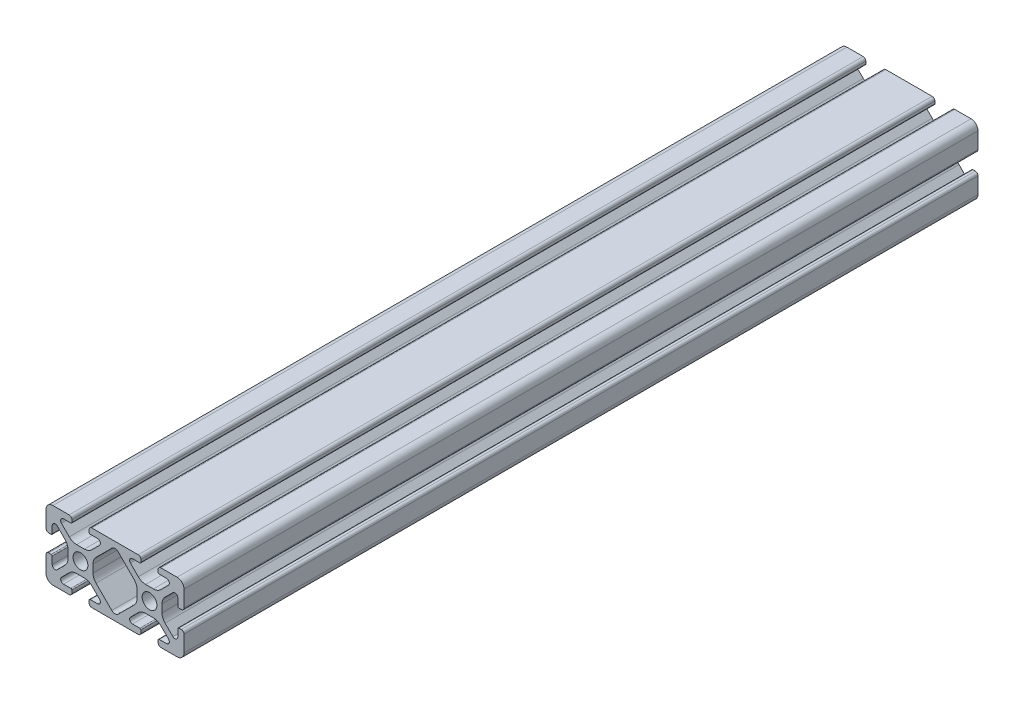
SolidWorks part; units mm, degrees
ref_plane "Front Plane" through (0, 0, 0) normal (0, 0, 1) x (1, 0, 0)
ref_plane "Top Plane" through (0, 0, 0) normal (0, 1, 0) x (1, 0, 0)
ref_plane "Right Plane" through (0, 0, 0) normal (1, 0, 0) x (0, 0, -1)
sketch "Sketch1" plane through (0, 0, 0) normal (0, 0, 1) x (1, 0, 0)
  line L2 (-19.9898, 7.9883) -> (-19.9898, 3.2893)
  line L3 (-17.9832, 9.9949) -> (-13.2842, 9.9949)
  line L4 (-12.4968, 9.2075) -> (-12.4968, 8.4963)
  line L5 (-12.8016, 8.1915) -> (-14.9098, 8.1915)
  line L6 (-15.5025, 6.7606) -> (-13.2477, 4.5058)
  line L7 (-16.7555, 5.5076) -> (-14.5007, 3.2528)
  line L8 (-18.1864, 4.9149) -> (-18.1864, 2.8067)
  line L9 (-18.4912, 2.5019) -> (-19.2024, 2.5019)
  line L11 (-11.1283, 3.6279) -> (-8.8615, 3.6279)
  line L12 (-13.6228, 1.1334) -> (-13.6228, -1.1334)
  line L13 (0, 9.9949) -> (-6.7056, 9.9949)
  line L14 (-7.493, 9.2075) -> (-7.493, 8.4963)
  line L15 (-7.1882, 8.1915) -> (-5.08, 8.1915)
  line L16 (-6.367, 1.1334) -> (-6.367, -1.1334)
  line L17 (-4.4873, 6.7606) -> (-6.7421, 4.5058)
  line L18 (-0.9396, 7.8023) -> (-5.4891, 3.2528)
  line L19 (-18.4912, -2.5019) -> (-19.2024, -2.5019)
  line L20 (-18.1864, -4.9149) -> (-18.1864, -2.8067)
  line L21 (-16.7555, -5.5076) -> (-14.5007, -3.2528)
  line L22 (-15.5025, -6.7606) -> (-13.2477, -4.5058)
  line L23 (-12.8016, -8.1915) -> (-14.9098, -8.1915)
  line L24 (-12.4968, -9.2075) -> (-12.4968, -8.4963)
  line L25 (-17.9832, -9.9949) -> (-13.2842, -9.9949)
  line L26 (-19.9898, -7.9883) -> (-19.9898, -3.2893)
  line L27 (0, -9.9949) -> (-6.7056, -9.9949)
  line L28 (-7.493, -9.2075) -> (-7.493, -8.4963)
  line L29 (-7.1882, -8.1915) -> (-5.08, -8.1915)
  line L30 (-4.4873, -6.7606) -> (-6.7421, -4.5058)
  line L31 (-0.9396, -7.8023) -> (-5.4891, -3.2528)
  line L32 (-11.1283, -3.6279) -> (-8.8615, -3.6279)
  line L34 (11.1283, -3.6279) -> (8.8615, -3.6279)
  line L35 (0.9396, -7.8023) -> (5.4891, -3.2528)
  line L36 (4.4873, -6.7606) -> (6.7421, -4.5058)
  line L37 (7.1882, -8.1915) -> (5.08, -8.1915)
  line L38 (7.493, -9.2075) -> (7.493, -8.4963)
  line L39 (0, -9.9949) -> (6.7056, -9.9949)
  line L40 (19.9898, -7.9883) -> (19.9898, -3.2893)
  line L41 (17.9832, -9.9949) -> (13.2842, -9.9949)
  line L42 (12.4968, -9.2075) -> (12.4968, -8.4963)
  line L43 (12.8016, -8.1915) -> (14.9098, -8.1915)
  line L44 (15.5025, -6.7606) -> (13.2477, -4.5058)
  line L45 (16.7555, -5.5076) -> (14.5007, -3.2528)
  line L46 (18.1864, -4.9149) -> (18.1864, -2.8067)
  line L47 (18.4912, -2.5019) -> (19.2024, -2.5019)
  line L48 (0.9396, 7.8023) -> (5.4891, 3.2528)
  line L49 (4.4873, 6.7606) -> (6.7421, 4.5058)
  line L50 (6.367, 1.1334) -> (6.367, -1.1334)
  line L51 (7.1882, 8.1915) -> (5.08, 8.1915)
  line L52 (7.493, 9.2075) -> (7.493, 8.4963)
  line L53 (0, 9.9949) -> (6.7056, 9.9949)
  line L54 (13.6228, 1.1334) -> (13.6228, -1.1334)
  line L55 (11.1283, 3.6279) -> (8.8615, 3.6279)
  line L56 (18.4912, 2.5019) -> (19.2024, 2.5019)
  line L57 (18.1864, 4.9149) -> (18.1864, 2.8067)
  line L58 (16.7555, 5.5076) -> (14.5007, 3.2528)
  line L59 (15.5025, 6.7606) -> (13.2477, 4.5058)
  line L60 (12.8016, 8.1915) -> (14.9098, 8.1915)
  line L61 (12.4968, 9.2075) -> (12.4968, 8.4963)
  line L62 (17.9832, 9.9949) -> (13.2842, 9.9949)
  line L63 (19.9898, 7.9883) -> (19.9898, 3.2893)
  circle A0 centre (-9.9949, 0) radius 2.1463
  arc A1 (-19.9898, 7.9883) -> (-17.9832, 9.9949) centre (-17.9832, 7.9883) cw
  arc A2 (-16.7555, 5.5076) -> (-18.1864, 4.9149) centre (-17.3482, 4.9149) ccw
  arc A3 (-14.9098, 8.1915) -> (-15.5025, 6.7606) centre (-14.9098, 7.3533) ccw
  arc A4 (-13.2842, 9.9949) -> (-12.4968, 9.2075) centre (-13.2842, 9.2075) cw
  arc A5 (-19.9898, 3.2893) -> (-19.2024, 2.5019) centre (-19.2024, 3.2893) ccw
  arc A6 (-18.1864, 2.8067) -> (-18.4912, 2.5019) centre (-18.4912, 2.8067) cw
  arc A7 (-12.4968, 8.4963) -> (-12.8016, 8.1915) centre (-12.8016, 8.4963) cw
  arc A8 (-11.1283, 3.6279) -> (-13.2477, 4.5058) centre (-11.1283, 6.6251) cw
  arc A9 (-13.6228, 1.1334) -> (-14.5007, 3.2528) centre (-16.62, 1.1334) ccw
  arc A10 (0.9396, 7.8023) -> (-0.9396, 7.8023) centre (0, 6.8627) ccw
  arc A11 (-0.9396, -7.8023) -> (0.9396, -7.8023) centre (0, -6.8627) ccw
  arc A12 (-6.7056, 9.9949) -> (-7.493, 9.2075) centre (-6.7056, 9.2075) ccw
  arc A13 (-7.493, 8.4963) -> (-7.1882, 8.1915) centre (-7.1882, 8.4963) ccw
  arc A14 (-8.8615, 3.6279) -> (-6.7421, 4.5058) centre (-8.8615, 6.6251) ccw
  arc A15 (-6.367, 1.1334) -> (-5.4891, 3.2528) centre (-3.3698, 1.1334) cw
  arc A16 (-5.08, 8.1915) -> (-4.4873, 6.7606) centre (-5.08, 7.3533) cw
  arc A17 (-13.6228, -1.1334) -> (-14.5007, -3.2528) centre (-16.62, -1.1334) cw
  arc A18 (-11.1283, -3.6279) -> (-13.2477, -4.5058) centre (-11.1283, -6.6251) ccw
  arc A19 (-12.4968, -8.4963) -> (-12.8016, -8.1915) centre (-12.8016, -8.4963) ccw
  arc A20 (-18.1864, -2.8067) -> (-18.4912, -2.5019) centre (-18.4912, -2.8067) ccw
  arc A21 (-19.9898, -3.2893) -> (-19.2024, -2.5019) centre (-19.2024, -3.2893) cw
  arc A22 (-13.2842, -9.9949) -> (-12.4968, -9.2075) centre (-13.2842, -9.2075) ccw
  arc A23 (-14.9098, -8.1915) -> (-15.5025, -6.7606) centre (-14.9098, -7.3533) cw
  arc A24 (-16.7555, -5.5076) -> (-18.1864, -4.9149) centre (-17.3482, -4.9149) cw
  arc A25 (-19.9898, -7.9883) -> (-17.9832, -9.9949) centre (-17.9832, -7.9883) ccw
  arc A26 (-5.08, -8.1915) -> (-4.4873, -6.7606) centre (-5.08, -7.3533) ccw
  arc A27 (-6.7056, -9.9949) -> (-7.493, -9.2075) centre (-6.7056, -9.2075) cw
  arc A28 (-7.493, -8.4963) -> (-7.1882, -8.1915) centre (-7.1882, -8.4963) cw
  arc A29 (-8.8615, -3.6279) -> (-6.7421, -4.5058) centre (-8.8615, -6.6251) cw
  arc A30 (-6.367, -1.1334) -> (-5.4891, -3.2528) centre (-3.3698, -1.1334) ccw
  arc A31 (6.367, -1.1334) -> (5.4891, -3.2528) centre (3.3698, -1.1334) cw
  arc A32 (8.8615, -3.6279) -> (6.7421, -4.5058) centre (8.8615, -6.6251) ccw
  arc A33 (7.493, -8.4963) -> (7.1882, -8.1915) centre (7.1882, -8.4963) ccw
  arc A34 (6.7056, -9.9949) -> (7.493, -9.2075) centre (6.7056, -9.2075) ccw
  arc A35 (5.08, -8.1915) -> (4.4873, -6.7606) centre (5.08, -7.3533) cw
  arc A36 (19.9898, -7.9883) -> (17.9832, -9.9949) centre (17.9832, -7.9883) cw
  arc A37 (16.7555, -5.5076) -> (18.1864, -4.9149) centre (17.3482, -4.9149) ccw
  arc A38 (14.9098, -8.1915) -> (15.5025, -6.7606) centre (14.9098, -7.3533) ccw
  arc A39 (13.2842, -9.9949) -> (12.4968, -9.2075) centre (13.2842, -9.2075) cw
  arc A40 (19.9898, -3.2893) -> (19.2024, -2.5019) centre (19.2024, -3.2893) ccw
  arc A41 (18.1864, -2.8067) -> (18.4912, -2.5019) centre (18.4912, -2.8067) cw
  arc A42 (12.4968, -8.4963) -> (12.8016, -8.1915) centre (12.8016, -8.4963) cw
  arc A43 (11.1283, -3.6279) -> (13.2477, -4.5058) centre (11.1283, -6.6251) cw
  arc A44 (13.6228, -1.1334) -> (14.5007, -3.2528) centre (16.62, -1.1334) ccw
  arc A45 (5.08, 8.1915) -> (4.4873, 6.7606) centre (5.08, 7.3533) ccw
  arc A46 (6.367, 1.1334) -> (5.4891, 3.2528) centre (3.3698, 1.1334) ccw
  arc A47 (8.8615, 3.6279) -> (6.7421, 4.5058) centre (8.8615, 6.6251) cw
  arc A48 (7.493, 8.4963) -> (7.1882, 8.1915) centre (7.1882, 8.4963) cw
  arc A49 (6.7056, 9.9949) -> (7.493, 9.2075) centre (6.7056, 9.2075) cw
  arc A50 (13.6228, 1.1334) -> (14.5007, 3.2528) centre (16.62, 1.1334) cw
  arc A51 (11.1283, 3.6279) -> (13.2477, 4.5058) centre (11.1283, 6.6251) ccw
  arc A52 (12.4968, 8.4963) -> (12.8016, 8.1915) centre (12.8016, 8.4963) ccw
  arc A53 (18.1864, 2.8067) -> (18.4912, 2.5019) centre (18.4912, 2.8067) ccw
  arc A54 (19.9898, 3.2893) -> (19.2024, 2.5019) centre (19.2024, 3.2893) cw
  arc A55 (13.2842, 9.9949) -> (12.4968, 9.2075) centre (13.2842, 9.2075) ccw
  arc A56 (14.9098, 8.1915) -> (15.5025, 6.7606) centre (14.9098, 7.3533) cw
  arc A57 (16.7555, 5.5076) -> (18.1864, 4.9149) centre (17.3482, 4.9149) cw
  arc A58 (19.9898, 7.9883) -> (17.9832, 9.9949) centre (17.9832, 7.9883) ccw
  circle A59 centre (9.9949, 0) radius 2.1463
  point P186 (9.9949, 3.6279)
extrude "Boss-Extrude1" add sketch "Sketch1" along normal mid plane 230
